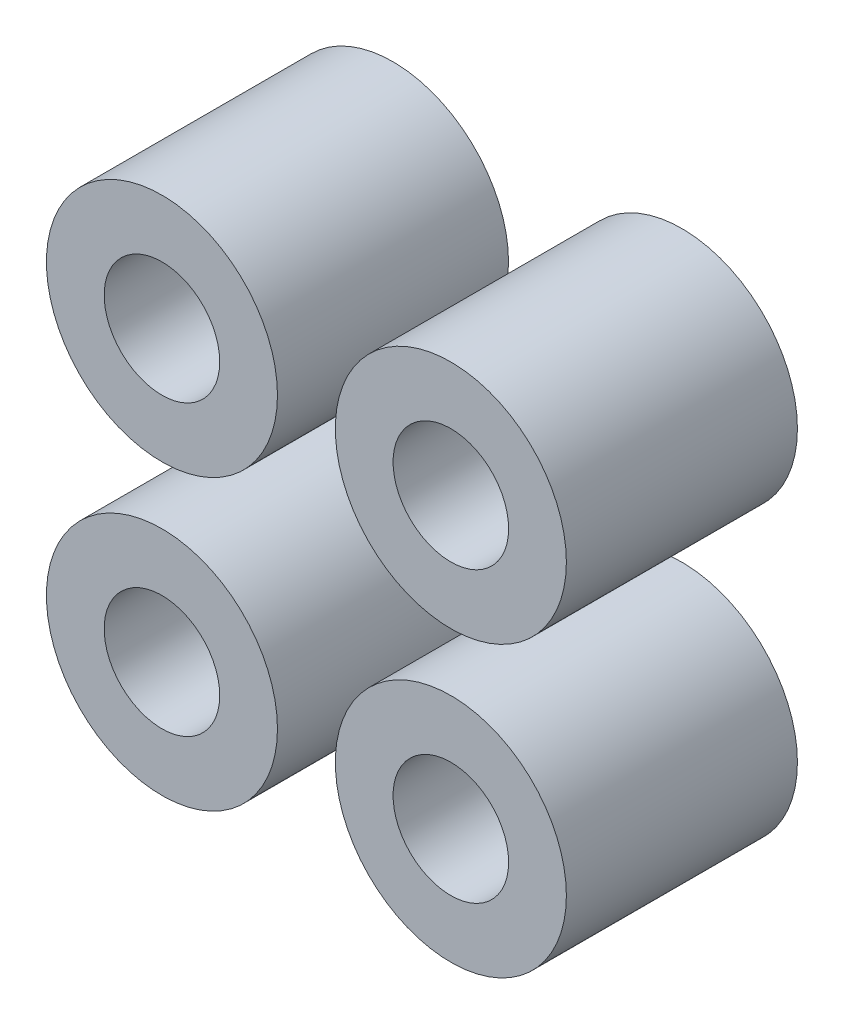
SolidWorks part; units mm, degrees
ref_plane "Front Plane" through (0, 0, 0) normal (0, 0, 1) x (1, 0, 0)
ref_plane "Top Plane" through (0, 0, 0) normal (0, 1, 0) x (1, 0, 0)
ref_plane "Right Plane" through (0, 0, 0) normal (1, 0, 0) x (0, 0, -1)
sketch "Sketch2" plane through (0, 0, 0) normal (0, 0, 1) x (1, 0, 0)
  line L1 (-7.5, -7.5) -> (7.5, -7.5) construction
  line L2 (-7.5, -7.5) -> (-7.5, 7.5) construction
  line L3 (-7.5, 7.5) -> (7.5, 7.5) construction
  line L4 (7.5, -7.5) -> (7.5, 7.5) construction
  line L5 (-7.5, -7.5) -> (7.5, 7.5) construction
  line L6 (-7.5, 7.5) -> (7.5, -7.5) construction
  circle A0 centre (-3.7512, 3.7512) radius 3
  circle A1 centre (-3.7512, 3.7512) radius 1.5
  circle A2 centre (3.7512, 3.7512) radius 3
  circle A3 centre (3.7512, 3.7512) radius 1.5
  circle A4 centre (3.7512, -3.7512) radius 3
  circle A5 centre (3.7512, -3.7512) radius 1.5
  circle A6 centre (-3.7512, -3.7512) radius 3
  circle A7 centre (-3.7512, -3.7512) radius 1.5
  point P0 (0, 0)
  dimension "D3" = 3
  dimension "D4" = 6
  dimension "D1" = 15
  dimension "D2" = 15
  dimension "D5" = 5.305
  dimension "D6" = 5.3016
  dimension "D7" = 4
extrude "Boss-Extrude1" add sketch "Sketch2" along normal blind 6
